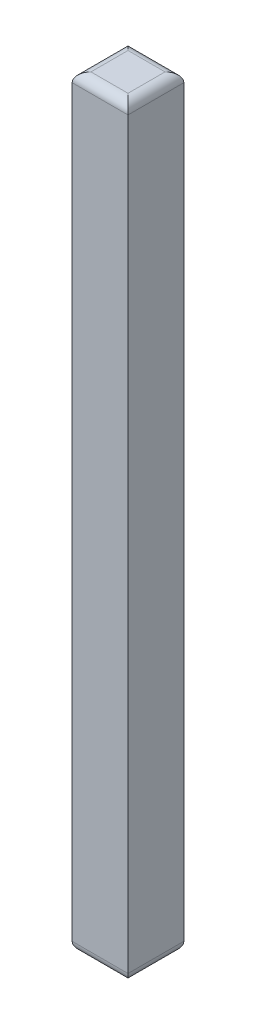
SolidWorks part; units mm, degrees
ref_plane "Front Plane" through (0, 0, 0) normal (0, 0, 1) x (1, 0, 0)
ref_plane "Top Plane" through (0, 0, 0) normal (0, 1, 0) x (1, 0, 0)
ref_plane "Right Plane" through (0, 0, 0) normal (1, 0, 0) x (0, 0, -1)
sketch "Sketch1" plane through (0, 0, 0) normal (0, 1, 0) x (1, 0, 0)
  line L1 (0, 0) -> (3.0226, 0)
  line L2 (0, 0) -> (0, 3.0226)
  line L3 (0, 3.0226) -> (3.0226, 3.0226)
  line L4 (3.0226, 0) -> (3.0226, 3.0226)
  dimension "D1" = 3.0226
  dimension "D2" = 3.0226
extrude "Boss-Extrude1" add sketch "Sketch1" along normal blind 41.275
fillet "Fillet1" radius 0.508 8 edges at (1.5113, 41.275, -3.0226) (3.0226, 41.275, -1.5113) (1.5113, 41.275, 0) (0, 41.275, -1.5113) (1.5113, 0, 0) (3.0226, 0, -1.5113) (1.5113, 0, -3.0226) (0, 0, -1.5113)
